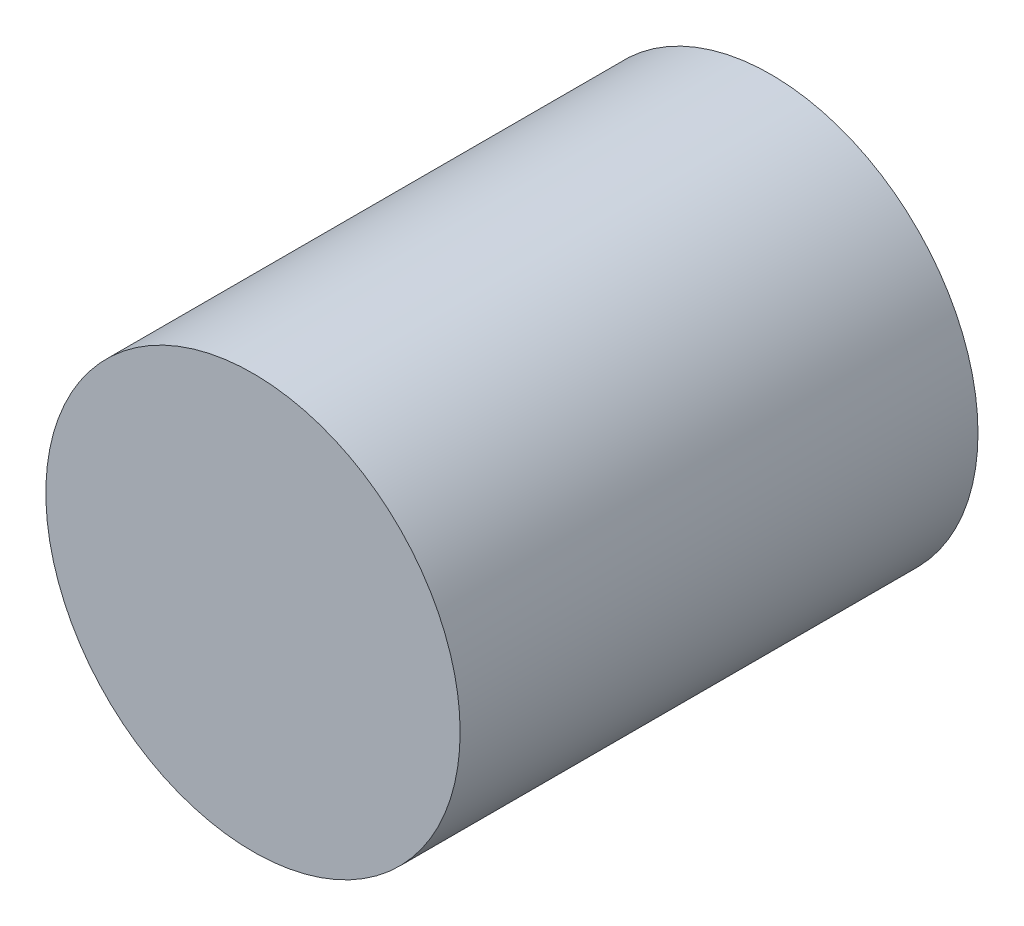
SolidWorks part; units mm, degrees
ref_plane "Front Plane" through (0, 0, 0) normal (0, 0, 1) x (1, 0, 0)
ref_plane "Top Plane" through (0, 0, 0) normal (0, 1, 0) x (1, 0, 0)
ref_plane "Right Plane" through (0, 0, 0) normal (1, 0, 0) x (0, 0, -1)
sketch "Sketch1" plane through (0, 0, 0) normal (0, 0, 1) x (1, 0, 0)
  circle A0 centre (-15.067, -8.8158) radius 40
  dimension "D1" = 80
extrude "Boss-Extrude1" add sketch "Sketch1" along normal blind 100
